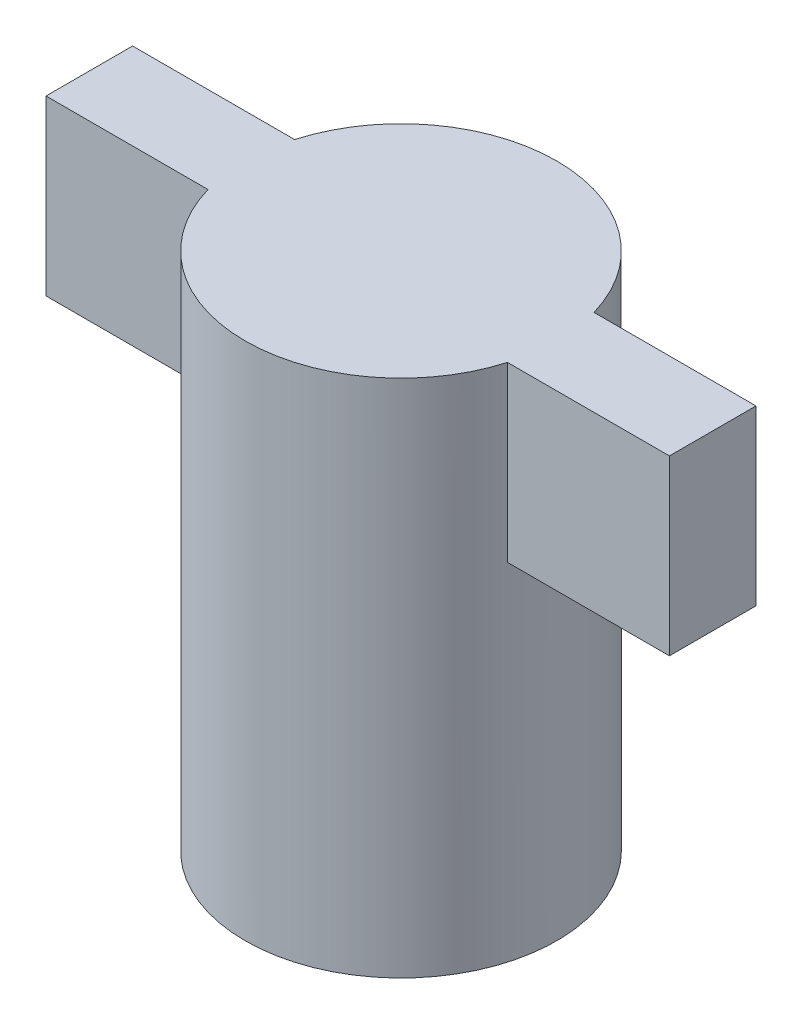
SolidWorks part; units mm, degrees
ref_plane "Front Plane" through (0, 0, 0) normal (0, 0, 1) x (1, 0, 0)
ref_plane "Top Plane" through (0, 0, 0) normal (0, 1, 0) x (1, 0, 0)
ref_plane "Right Plane" through (0, 0, 0) normal (1, 0, 0) x (0, 0, -1)
sketch "Sketch2" plane through (0, 0, 0) normal (0, 1, 0) x (1, 0, 0)
  circle A0 centre (0, 0) radius 4.5
  dimension "D1" = 9
extrude "Boss-Extrude1" add sketch "Sketch2" along normal blind 15
sketch "Sketch4" plane through (0, 0, 0) normal (0, -1, 0) x (1, 0, 0)
  circle A0 centre (0, 0.0092) radius 4
  dimension "D1" = 8
extrude "Cut-Extrude2" cut sketch "Sketch4" against normal blind 1.5
sketch "Sketch5" plane through (0, 1.5, 0) normal (0, -1, 0) x (1, 0, 0)
  circle A0 centre (0.0061, -0.0092) radius 3
  dimension "D1" = 6
extrude "Cut-Extrude3" cut sketch "Sketch5" against normal blind 2.5
sketch "Sketch6" plane through (0, 4, 0) normal (0, -1, 0) x (1, 0, 0)
  line L0 (-2.4462, -1.7395) -> (2.4415, -1.7395)
  line L1 (-2.4462, 1.7405) -> (2.4415, 1.7405)
  line L2 (-2.4462, -1.7395) -> (2.4415, 1.7405) construction
  line L3 (-2.4462, 1.7405) -> (2.4415, -1.7395) construction
  arc A0 (-2.4462, 1.7405) -> (-2.4462, -1.7395) centre (-0.0023, 0.0005) ccw
  arc A1 (2.4415, 1.7405) -> (2.4415, -1.7395) centre (-0.0023, 0.0005) cw
  point P0 (-0.0023, 0.0005)
extrude "Cut-Extrude4" cut sketch "Sketch6" against normal blind 6
sketch "Sketch7" plane through (0, 15, 0) normal (0, 1, 0) x (1, 0, 0)
  line L1 (-9, 1.25) -> (9, 1.25)
  line L2 (-9, 1.25) -> (-9, -1.25)
  line L3 (-9, -1.25) -> (9, -1.25)
  line L4 (9, 1.25) -> (9, -1.25)
  line L5 (-9, 1.25) -> (9, -1.25) construction
  line L6 (-9, -1.25) -> (9, 1.25) construction
  point P0 (0, 0)
  dimension "D1" = 2.5
  dimension "D2" = 18
extrude "Boss-Extrude2" add sketch "Sketch7" against normal blind 5
